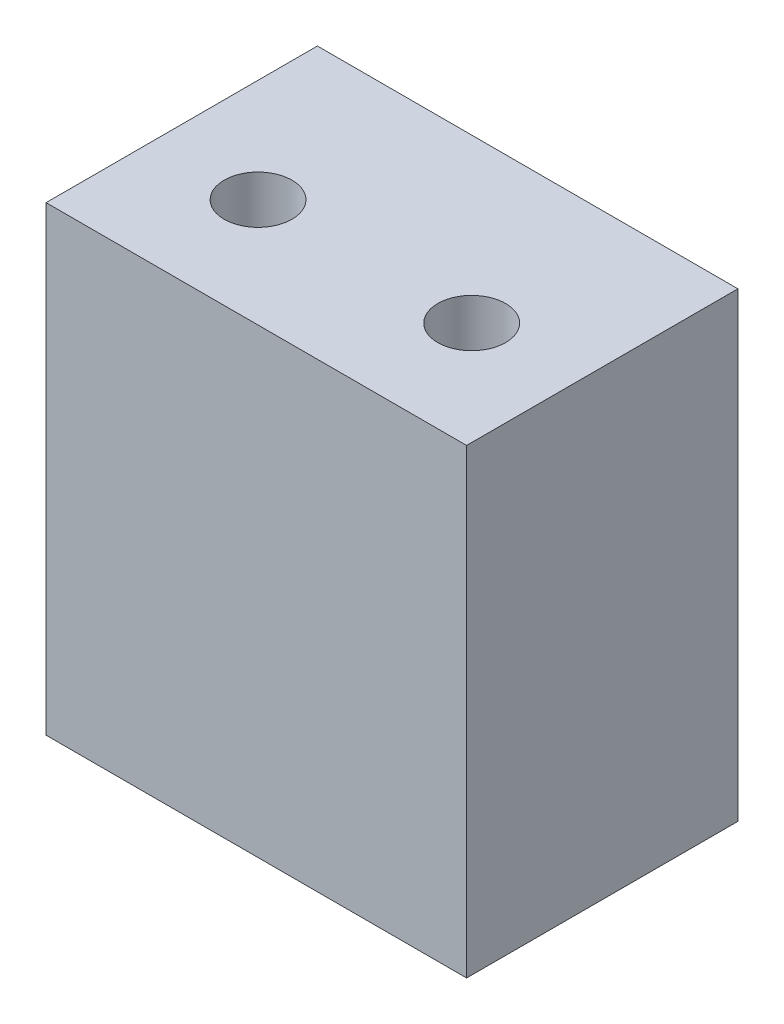
SolidWorks part; units mm, degrees
material "Maple"
ref_plane "Front Plane" through (0, 0, 0) normal (0, 0, 1) x (1, 0, 0)
ref_plane "Top Plane" through (0, 0, 0) normal (0, 1, 0) x (1, 0, 0)
ref_plane "Right Plane" through (0, 0, 0) normal (1, 0, 0) x (0, 0, -1)
sketch "Sketch1" plane through (0, 0, 0) normal (0, 0, 1) x (1, 0, 0)
  line L1 (9.8425, -10.795) -> (-9.8425, -10.795)
  line L2 (9.8425, -10.795) -> (9.8425, 10.795)
  line L3 (9.8425, 10.795) -> (-9.8425, 10.795)
  line L4 (-9.8425, -10.795) -> (-9.8425, 10.795)
  line L5 (9.8425, -10.795) -> (-9.8425, 10.795) construction
  line L6 (9.8425, 10.795) -> (-9.8425, -10.795) construction
  point P0 (0, 0)
  dimension "D1" = 21.59
  dimension "D2" = 19.685
extrude "Boss-Extrude1" add sketch "Sketch1" along normal blind 12.7
sketch "Sketch7" plane through (0, 10.795, 0) normal (0, 1, 0) x (1, 0, 0)
  line L0 (9.8425, -6.35) -> (-9.8425, -6.35) construction
  line L1 (9.8425, -12.7) -> (9.8425, 0) construction
  line L2 (-9.8425, -12.7) -> (-9.8425, 0) construction
  line L3 (0, -12.7) -> (0, 0) construction
  line L4 (9.8425, -12.7) -> (-9.8425, -12.7) construction
  line L5 (9.8425, 0) -> (-9.8425, 0) construction
  circle A0 centre (5, -7.62) radius 1.5875
  circle A1 centre (-5, -7.62) radius 1.5875
  dimension "D1" = 3.175
  dimension "D2" = 1.27
  dimension "D3" = 5
extrude "Cut-Extrude1" cut sketch "Sketch7" against normal blind 6.35
